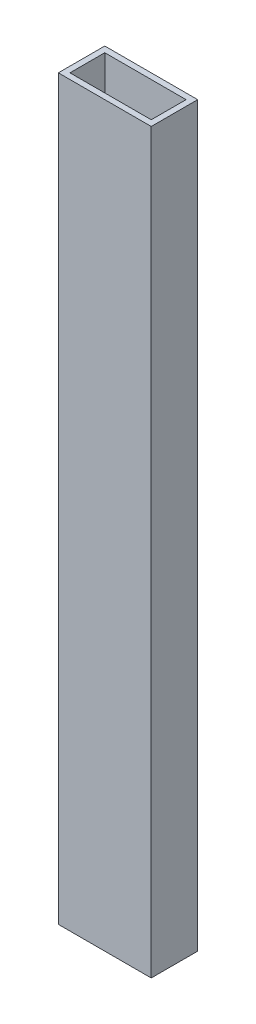
SolidWorks part; units mm, degrees
ref_plane "Front Plane" through (0, 0, 0) normal (0, 0, 1) x (1, 0, 0)
ref_plane "Top Plane" through (0, 0, 0) normal (0, 1, 0) x (1, 0, 0)
ref_plane "Right Plane" through (0, 0, 0) normal (1, 0, 0) x (0, 0, -1)
sketch "Sketch1" plane through (0, 0, 0) normal (0, 1, 0) x (1, 0, 0)
  line L1 (0, 0) -> (50.8, 0)
  line L2 (0, 0) -> (0, 25.4)
  line L3 (0, 25.4) -> (50.8, 25.4)
  line L4 (50.8, 0) -> (50.8, 25.4)
  line L5 (3.175, 22.225) -> (47.625, 22.225)
  line L6 (3.175, 22.225) -> (3.175, 3.175)
  line L7 (3.175, 3.175) -> (47.625, 3.175)
  line L8 (47.625, 22.225) -> (47.625, 3.175)
  dimension "D1" = 3.175
  dimension "D2" = 3.175
  dimension "D3" = 3.175
  dimension "D4" = 3.175
  dimension "D5" = 50.8
  dimension "D6" = 25.4
extrude "Boss-Extrude1" add sketch "Sketch1" along normal blind 403.225
